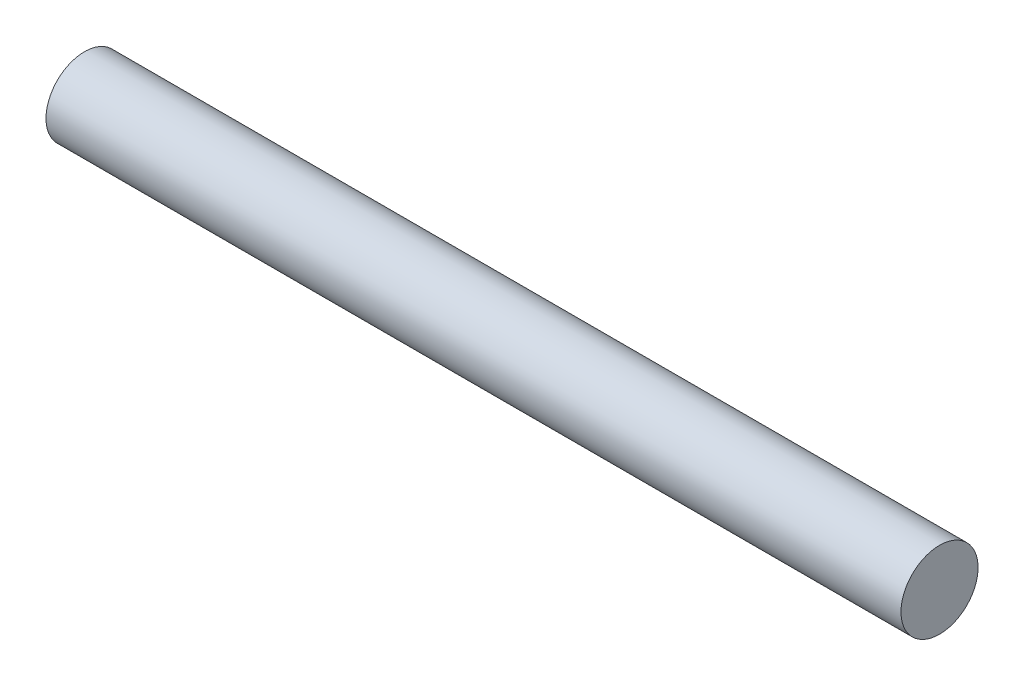
SolidWorks part; units mm, degrees
material "Maple"
ref_plane "Front Plane" through (0, 0, 0) normal (0, 0, 1) x (1, 0, 0)
ref_plane "Top Plane" through (0, 0, 0) normal (0, 1, 0) x (1, 0, 0)
ref_plane "Right Plane" through (0, 0, 0) normal (1, 0, 0) x (0, 0, -1)
sketch "Sketch1" plane through (0, 0, 0) normal (0, 0, 1) x (1, 0, 0)
  line L0 (-28.2483, 0) -> (25.3267, 0)
  line L1 (25.3267, 0) -> (25.3267, 2.415)
  line L2 (25.3267, 2.415) -> (-28.2483, 2.415)
  line L3 (-28.2483, 2.415) -> (-28.2483, 0)
  dimension "D1" = 53.575
  dimension "D2" = 2.415
revolve "Revolve1" add sketch "Sketch1" angle 360 about L0
equation "\"length\"=53.575"
equation "\"D1@Sketch1\"=\"length\""
equation "\"width\"=2.415"
equation "\"D2@Sketch1\"=\"width\""
